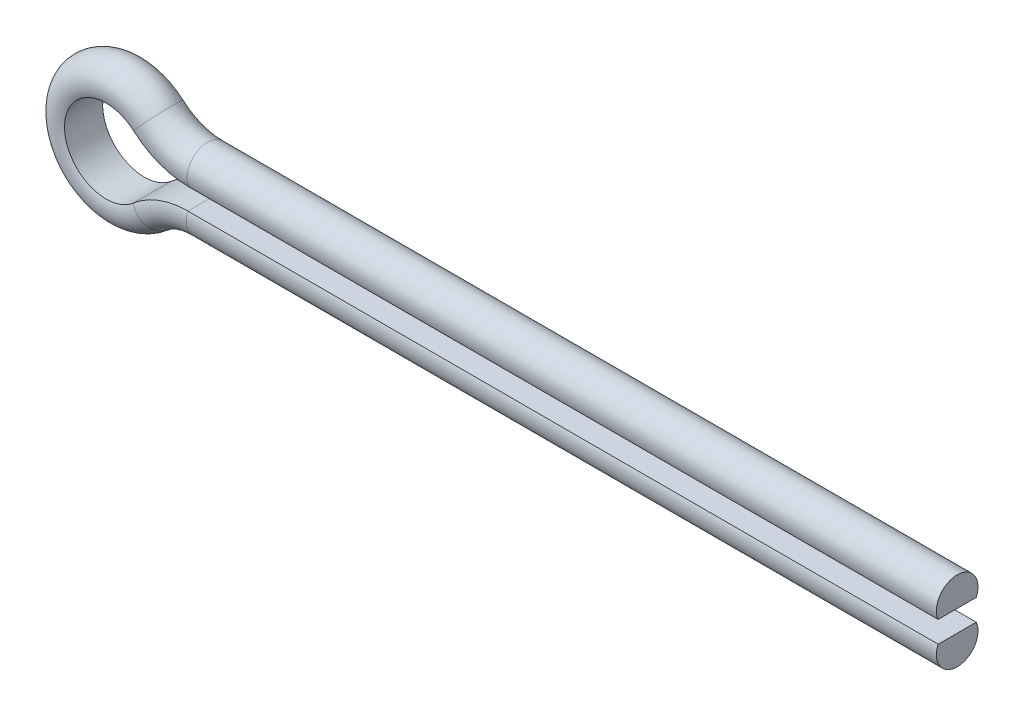
SolidWorks part; units mm, degrees
ref_plane "Front Plane" through (0, 0, 0) normal (0, 0, 1) x (1, 0, 0)
ref_plane "Top Plane" through (0, 0, 0) normal (0, 1, 0) x (1, 0, 0)
ref_plane "Right Plane" through (0, 0, 0) normal (1, 0, 0) x (0, 0, -1)
sketch "Sketch1" plane through (0, 0, 0) normal (0, 0, 1) x (1, 0, 0)
  line L0 (0, 0) -> (-90.0784, 0)
  line L1 (-90.1683, -2.5787) -> (0, -2.5787)
  arc A0 (-90.0784, 0) -> (-96.6928, 2.5) centre (-90.0784, 10) cw
  arc A1 (-96.6928, 2.5) -> (-96.7228, -5.0262) centre (-100, -1.25) ccw
  arc A2 (-96.7228, -5.0262) -> (-90.1683, -2.5787) centre (-90.1683, -12.5787) cw
  point P9 (-93.614, 0.6459)
  point P11 (-100, -3.559)
  point P12 (-90.0784, -2.5787)
  point P13 (0, 0)
  dimension "D2" = 5
  dimension "D4" = 1.25
  dimension "D1" = 100
  dimension "D3" = 10
  dimension "D5" = 0
sketch "Sketch2" plane through (0, 0, 0) normal (1, 0, 0) x (0, 0, -1)
  line L0 (2.2913, 0) -> (-2.2913, 0)
  arc A0 (-2.2913, 0) -> (2.2913, 0) centre (0, 1) cw
  point P4 (0, 0)
  point P5 (0, 3.5)
  dimension "D2" = 2.5
  dimension "D1" = 3.5
sweep "Sweep1" add profiles "Sketch2" path "Sketch1"
